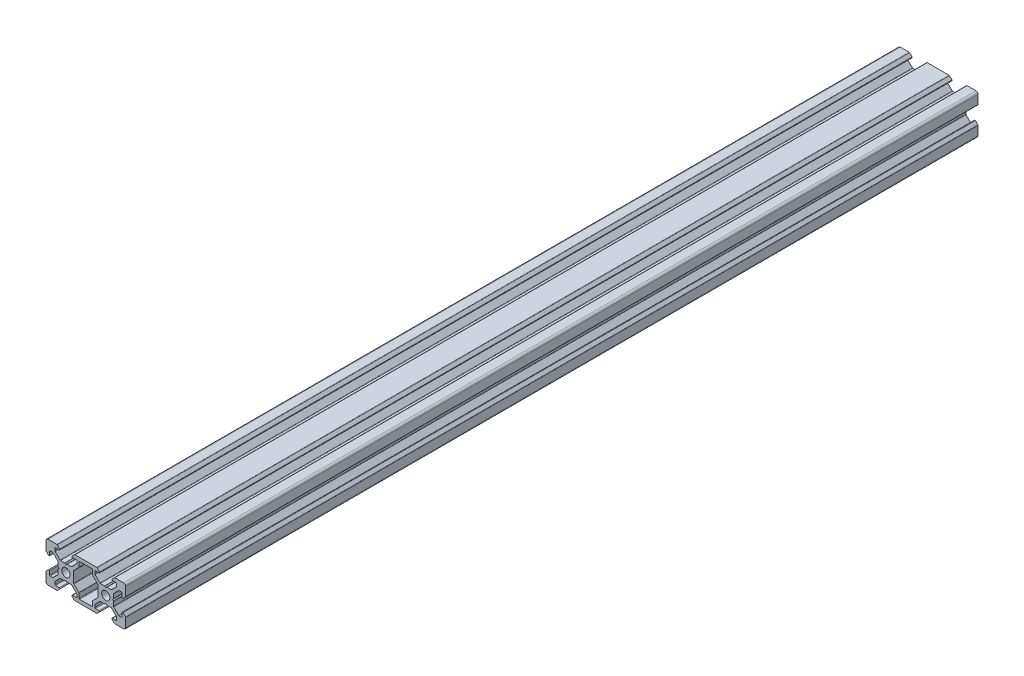
SolidWorks part; units mm, degrees
material "АД31Т ГОСТ 4784-97"
ref_plane "Спереди" through (0, 0, 0) normal (0, 0, 1) x (1, 0, 0)
ref_plane "Сверху" through (0, 0, 0) normal (0, 1, 0) x (1, 0, 0)
ref_plane "Справа" through (0, 0, 0) normal (1, 0, 0) x (0, 0, -1)
sketch "Эскиз1" plane through (0, 0, 0) normal (0, 0, 1) x (1, 0, 0)
  line L0 (12.9654, 0) -> (-12.9654, 0) construction
  line L1 (0, -12.9654) -> (0, 12.9654) construction
  line L2 (0, 0) -> (-18.3359, -18.3359) construction
  line L3 (-10, -10) -> (-10, -4.4)
  line L4 (-10, -4.4) -> (-8.2, -2.6)
  line L5 (-8.2, -2.6) -> (-8.2, -5.4993)
  line L6 (-8.2, -5.4993) -> (-6.56, -5.4993)
  line L7 (-6.56, -5.4993) -> (-3.9007, -2.84)
  line L8 (-3.9007, -2.84) -> (-3.9007, -0.5)
  line L9 (-3.9007, -0.5) -> (-3.4007, 0)
  line L10 (-0.5, -3.9007) -> (0, -3.4007)
  line L11 (-2.84, -3.9007) -> (-0.5, -3.9007)
  line L12 (-5.4993, -6.56) -> (-2.84, -3.9007)
  line L13 (-5.4993, -8.2) -> (-5.4993, -6.56)
  line L14 (-2.6, -8.2) -> (-5.4993, -8.2)
  line L15 (-4.4, -10) -> (-2.6, -8.2)
  line L16 (-10, -10) -> (-4.4, -10)
  line L17 (-10, 10) -> (-4.4, 10)
  line L18 (-4.4, 10) -> (-2.6, 8.2)
  line L19 (-2.6, 8.2) -> (-5.4993, 8.2)
  line L20 (-5.4993, 8.2) -> (-5.4993, 6.56)
  line L21 (-5.4993, 6.56) -> (-2.84, 3.9007)
  line L22 (-2.84, 3.9007) -> (-0.5, 3.9007)
  line L23 (-0.5, 3.9007) -> (0, 3.4007)
  line L24 (-3.9007, 0.5) -> (-3.4007, 0)
  line L25 (-3.9007, 2.84) -> (-3.9007, 0.5)
  line L26 (-6.56, 5.4993) -> (-3.9007, 2.84)
  line L27 (-8.2, 5.4993) -> (-6.56, 5.4993)
  line L28 (-8.2, 2.6) -> (-8.2, 5.4993)
  line L29 (-10, 4.4) -> (-8.2, 2.6)
  line L30 (-10, 10) -> (-10, 4.4)
  line L31 (0.5, 3.9007) -> (0, 3.4007)
  line L32 (0.5, -3.9007) -> (0, -3.4007)
  line L33 (10, -10) -> (10, 10) construction
  line L34 (3.9007, -0.5) -> (3.9007, 0.5)
  line L35 (6.56, -5.4993) -> (6.56, -8.2)
  line L36 (13.44, -5.4993) -> (16.0993, -2.84)
  line L37 (6.56, 5.4993) -> (3.9007, 2.84)
  line L38 (3.9007, 2.84) -> (3.9007, 0.5)
  line L39 (6.56, -8.2) -> (13.44, -8.2)
  line L40 (2.84, 3.9007) -> (0.5, 3.9007)
  line L41 (5.4993, 6.56) -> (2.84, 3.9007)
  line L42 (5.4993, 8.2) -> (5.4993, 6.56)
  line L43 (2.6, 8.2) -> (5.4993, 8.2)
  line L44 (4.4, 10) -> (2.6, 8.2)
  line L45 (15.6, 10) -> (4.4, 10)
  line L46 (15.6, -10) -> (4.4, -10)
  line L47 (4.4, -10) -> (2.6, -8.2)
  line L48 (2.6, -8.2) -> (5.4993, -8.2)
  line L49 (5.4993, -8.2) -> (5.4993, -6.56)
  line L50 (5.4993, -6.56) -> (2.84, -3.9007)
  line L51 (2.84, -3.9007) -> (0.5, -3.9007)
  line L52 (6.56, 5.4993) -> (6.56, 8.2)
  line L53 (3.9007, -2.84) -> (3.9007, -0.5)
  line L54 (6.56, -5.4993) -> (3.9007, -2.84)
  line L55 (16.0993, -2.84) -> (16.0993, -0.5)
  line L56 (6.56, 8.2) -> (13.44, 8.2)
  line L57 (13.44, 5.4993) -> (13.44, 8.2)
  line L58 (17.16, -3.9007) -> (19.5, -3.9007)
  line L59 (14.5007, -6.56) -> (17.16, -3.9007)
  line L60 (14.5007, -8.2) -> (14.5007, -6.56)
  line L61 (17.4, -8.2) -> (14.5007, -8.2)
  line L62 (15.6, -10) -> (17.4, -8.2)
  line L63 (15.6, 10) -> (17.4, 8.2)
  line L64 (17.4, 8.2) -> (14.5007, 8.2)
  line L65 (14.5007, 8.2) -> (14.5007, 6.56)
  line L66 (14.5007, 6.56) -> (17.16, 3.9007)
  line L67 (17.16, 3.9007) -> (19.5, 3.9007)
  line L68 (16.0993, 2.84) -> (16.0993, 0.5)
  line L69 (13.44, 5.4993) -> (16.0993, 2.84)
  line L70 (13.44, -5.4993) -> (13.44, -8.2)
  line L71 (16.0993, -0.5) -> (16.0993, 0.5)
  line L72 (19.5, -3.9007) -> (20, -3.4007)
  line L73 (19.5, 3.9007) -> (20, 3.4007)
  line L74 (30, 10) -> (30, 4.4)
  line L75 (30, 4.4) -> (28.2, 2.6)
  line L76 (28.2, 2.6) -> (28.2, 5.4993)
  line L77 (28.2, 5.4993) -> (26.56, 5.4993)
  line L78 (26.56, 5.4993) -> (23.9007, 2.84)
  line L79 (23.9007, 2.84) -> (23.9007, 0.5)
  line L80 (23.9007, 0.5) -> (23.4007, 0)
  line L81 (20.5, 3.9007) -> (20, 3.4007)
  line L82 (22.84, 3.9007) -> (20.5, 3.9007)
  line L83 (25.4993, 6.56) -> (22.84, 3.9007)
  line L84 (25.4993, 8.2) -> (25.4993, 6.56)
  line L85 (22.6, 8.2) -> (25.4993, 8.2)
  line L86 (24.4, 10) -> (22.6, 8.2)
  line L87 (30, 10) -> (24.4, 10)
  line L88 (30, -10) -> (24.4, -10)
  line L89 (24.4, -10) -> (22.6, -8.2)
  line L90 (22.6, -8.2) -> (25.4993, -8.2)
  line L91 (25.4993, -8.2) -> (25.4993, -6.56)
  line L92 (25.4993, -6.56) -> (22.84, -3.9007)
  line L93 (22.84, -3.9007) -> (20.5, -3.9007)
  line L94 (20.5, -3.9007) -> (20, -3.4007)
  line L95 (23.9007, -0.5) -> (23.4007, 0)
  line L96 (23.9007, -2.84) -> (23.9007, -0.5)
  line L97 (26.56, -5.4993) -> (23.9007, -2.84)
  line L98 (28.2, -5.4993) -> (26.56, -5.4993)
  line L99 (28.2, -2.6) -> (28.2, -5.4993)
  line L100 (30, -4.4) -> (28.2, -2.6)
  line L101 (30, -10) -> (30, -4.4)
  circle A0 centre (0, 0) radius 2.1
  circle A1 centre (20, 0) radius 2.1
  point P62 (10, 8.2)
  point P80 (10, -8.2)
  dimension "D5" = 2.6
  dimension "D10" = 4.2
  dimension "D2" = 10
  dimension "D3" = 1.64
  dimension "D4" = 1.5
  dimension "D6" = 1.8
  dimension "D7" = 2.84
  dimension "D8" = 0.5
  dimension "D9" = 45
extrude "Бобышка-Вытянуть1" add sketch "Эскиз1" along a picked direction on the side of the normal blind 428
fillet "Скругление1" radius 1 4 edges at (-10, 10, 214) (-10, -10, 214) (30, 10, 214) (30, -10, 214)
fillet "Скругление2" radius 0.3 83 edges at (-4.4, 10, 214) (-2.6, 8.2, 214) (-5.4993, 8.2, 214) (-5.4993, 6.56, 214) (-2.84, 3.9007, 214) (-0.5, 3.9007, 214) (0.5, 3.9007, 214) (2.84, 3.9007, 214) (5.4993, 6.56, 214) (4.4, 10, 214) (5.4993, 8.2, 214) (2.6, 8.2, 214) (3.9007, 2.84, 214) (3.9007, -2.84, 214) (6.56, -5.4993, 214) (4.4, -10, 214) (2.6, -8.2, 214) (5.4993, -8.2, 214) (5.4993, -6.56, 214) (2.84, -3.9007, 214) (0.5, -3.9007, 214) (-0.5, -3.9007, 214) (-2.84, -3.9007, 214) (-5.4993, -6.56, 214) (-5.4993, -8.2, 214) (-2.6, -8.2, 214) (-10, -4.4, 214) (-8.2, -2.6, 214) (-8.2, -5.4993, 214) (-6.56, -5.4993, 214) (-3.9007, -2.84, 214) (-3.9007, -0.5, 214) (-3.9007, 0.5, 214) (-3.9007, 2.84, 214) (-6.56, 5.4993, 214) (-8.2, 5.4993, 214) (-8.2, 2.6, 214) (-10, 4.4, 214) (6.56, 5.4993, 214) (6.56, 8.2, 214) (13.44, 8.2, 214) (13.44, 5.4993, 214) (16.0993, 2.84, 214) (13.44, -5.4993, 214) (16.0993, -2.84, 214) (13.44, -8.2, 214) (6.56, -8.2, 214) (15.6, 10, 214) (17.4, 8.2, 214) (14.5007, 8.2, 214) (14.5007, 6.56, 214) (17.16, 3.9007, 214) (19.5, 3.9007, 214) (20.5, 3.9007, 214) (22.84, 3.9007, 214) (25.4993, 6.56, 214) (25.4993, 8.2, 214) (22.6, 8.2, 214) (24.4, 10, 214) (30, 4.4, 214) (28.2, 2.6, 214) (28.2, 5.4993, 214) (26.56, 5.4993, 214) (23.9007, 2.84, 214) (23.9007, 0.5, 214) (23.9007, -0.5, 214) (23.9007, -2.84, 214) (26.56, -5.4993, 214) (28.2, -5.4993, 214) (28.2, -2.6, 214) (30, -4.4, 214) (24.4, -10, 214) (22.6, -8.2, 214) (25.4993, -8.2, 214) (25.4993, -6.56, 214) (22.84, -3.9007, 214) (20.5, -3.9007, 214) (19.5, -3.9007, 214) (17.16, -3.9007, 214) (14.5007, -6.56, 214) (14.5007, -8.2, 214) (17.4, -8.2, 214) (15.6, -10, 214)
